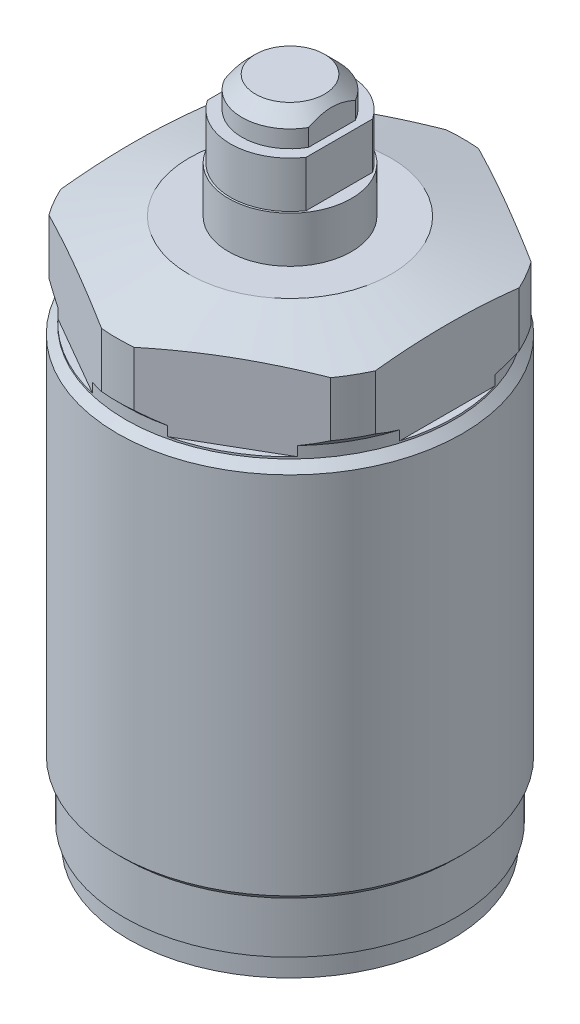
SolidWorks part; units mm, degrees
material "Alloy Steel"
ref_plane "Front Plane" through (0, 0, 0) normal (0, 0, 1) x (1, 0, 0)
ref_plane "Top Plane" through (0, 0, 0) normal (0, 1, 0) x (1, 0, 0)
ref_plane "Right Plane" through (0, 0, 0) normal (1, 0, 0) x (0, 0, -1)
sketch "Sketch1" plane through (0, 0, 0) normal (0, 0, 1) x (1, 0, 0)
  line L0 (0, 0) -> (0, -9.6761) construction
  line L1 (-21.575, 0) -> (-21, 0)
  line L2 (-21.575, 0) -> (-21.575, 6.65)
  line L3 (-21.575, 6.65) -> (-22.425, 7.5)
  line L4 (-22.425, 7.5) -> (-22.425, 54.95)
  line L5 (-22.425, 54.95) -> (-21.375, 56)
  line L6 (-21.375, 56) -> (-21.375, 57.5)
  line L7 (-21.375, 57.5) -> (-22.5, 58.625)
  line L8 (-22.5, 58.625) -> (-22.5, 65.738)
  line L9 (-22.5, 65.738) -> (-13.125, 68.25)
  line L10 (-13.125, 68.25) -> (0, 68.25)
  line L11 (0, 68.25) -> (0, -2.75)
  line L12 (-21, 0) -> (-21, -2.75)
  line L13 (-21, -2.75) -> (0, -2.75)
  dimension "D1" = 43.15
  dimension "D2" = 9.4
  dimension "D3" = 2.75
  dimension "D4" = 42
  dimension "D5" = 45
  dimension "D6" = 44.85
  dimension "D7" = 71
  dimension "D8" = 15
  dimension "D9" = 26.25
  dimension "D10" = 45
  dimension "D11" = 12.25
  dimension "D12" = 42.75
  dimension "D13" = 1.5
revolve "Revolve1" add sketch "Sketch1" angle 360 about L0
sketch "Sketch2" plane through (0, 68.25, 0) normal (0, 1, 0) x (1, 0, 0)
  line L1 (0, 23.6252) -> (-20.46, 11.8126)
  line L2 (-20.46, 11.8126) -> (-20.46, -11.8126)
  line L3 (-20.46, -11.8126) -> (0, -23.6252)
  line L4 (0, -23.6252) -> (20.46, -11.8126)
  line L5 (20.46, -11.8126) -> (20.46, 11.8126)
  line L6 (20.46, 11.8126) -> (0, 23.6252)
  circle A0 centre (0, 0) radius 20.46 construction
  dimension "D1" = 40.92
extrude "Cut-Extrude1" cut sketch "Sketch2" against normal blind 12 flip side to cut
sketch "Sketch4" plane through (0, 0, 0) normal (0, 0, 1) x (1, 0, 0)
  line L0 (0, 0) -> (0, 85.9979) construction
  line L1 (0, 84.25) -> (-6.25, 84.25)
  line L2 (-6.25, 84.25) -> (-6.25, 80.262)
  line L3 (-6.25, 80.262) -> (-7.745, 80.262)
  line L4 (-7.745, 80.262) -> (-7.745, 74.242)
  line L5 (-7.745, 74.242) -> (-8, 74.242)
  line L6 (-8, 74.242) -> (-8, 68.25)
  line L7 (13.125, 68.25) -> (-13.125, 68.25) construction
  line L8 (-8, 68.25) -> (0, 68.25)
  line L9 (0, 68.25) -> (0, 84.25)
  line L10 (-21, -2.75) -> (21, -2.75) construction
  dimension "D1" = 87
  dimension "D2" = 3.988
  dimension "D3" = 12.5
  dimension "D4" = 16
  dimension "D5" = 15.49
  dimension "D6" = 10.008
revolve "Revolve2" add sketch "Sketch4" angle 360 about L0
chamfer "Chamfer1" distance 1.754 angle 45 1 edges at (0, 84.25, -6.25)
sketch "Sketch5" plane through (0, 0, 0) normal (0, 0, 1) x (1, 0, 0)
  line L0 (7.745, 80.262) -> (-7.745, 80.262) construction
  line L1 (-5.46, 80.262) -> (-7.745, 80.262)
  line L2 (-5.46, 80.262) -> (-5.46, 84.25)
  line L3 (-5.46, 84.25) -> (-7.745, 84.25)
  line L4 (-7.745, 80.262) -> (-7.745, 84.25)
  line L5 (4.496, 84.25) -> (-4.496, 84.25) construction
  line L6 (-7.745, 80.262) -> (-7.745, 74.242) construction
  line L7 (0, 0) -> (0, 109.405) construction
  line L8 (7.745, 80.262) -> (7.745, 84.25)
  line L9 (5.46, 84.25) -> (7.745, 84.25)
  line L10 (5.46, 80.262) -> (5.46, 84.25)
  line L11 (5.46, 80.262) -> (7.745, 80.262)
  dimension "D1" = 10.92
extrude "Cut-Extrude2" cut sketch "Sketch5" against normal through all and the other way through all
sketch "Sketch6" plane through (0, 0, 0) normal (0, 0, 1) x (1, 0, 0)
  line L0 (7.745, 80.262) -> (-7.745, 80.262) construction
  line L1 (-6.425, 80.262) -> (-8, 80.262)
  line L2 (-6.425, 80.262) -> (-6.425, 74.242)
  line L3 (-6.425, 74.242) -> (-8, 74.242)
  line L4 (-8, 80.262) -> (-8, 74.242)
  line L5 (0, 0) -> (0, 83.5625) construction
  line L6 (8, 80.262) -> (8, 74.242)
  line L7 (6.425, 74.242) -> (8, 74.242)
  line L8 (6.425, 80.262) -> (6.425, 74.242)
  line L9 (6.425, 80.262) -> (8, 80.262)
  dimension "D1" = 12.85
extrude "Cut-Extrude3" cut sketch "Sketch6" against normal through all and the other way through all
